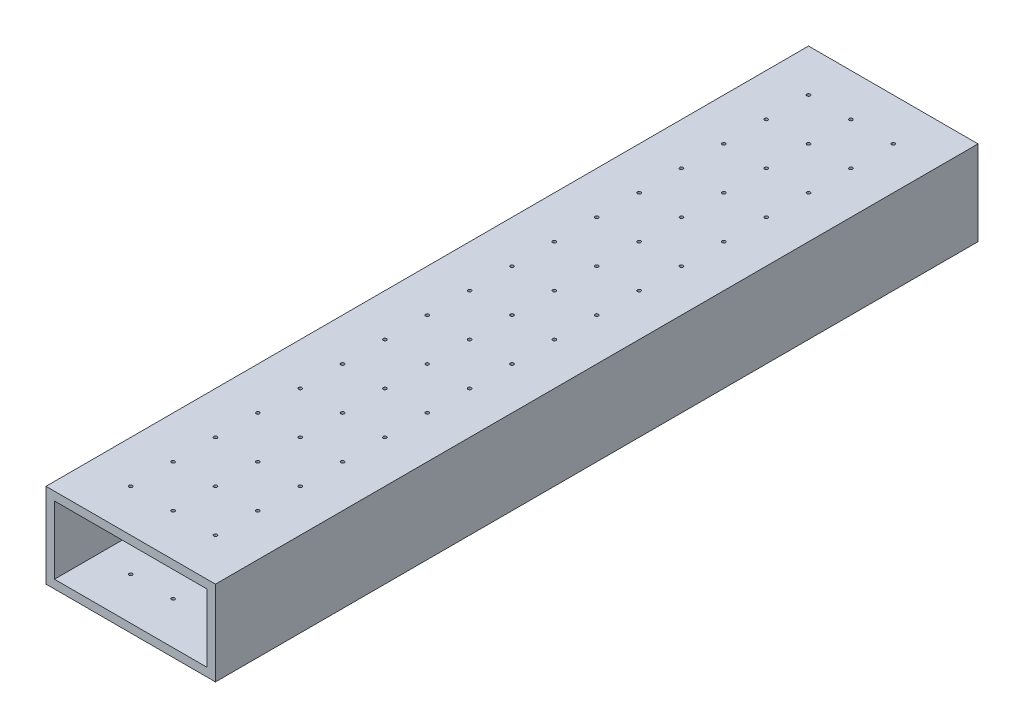
SolidWorks part; units mm, degrees
ref_plane "Front Plane" through (0, 0, 0) normal (0, 0, 1) x (1, 0, 0)
ref_plane "Top Plane" through (0, 0, 0) normal (0, 1, 0) x (1, 0, 0)
ref_plane "Right Plane" through (0, 0, 0) normal (1, 0, 0) x (0, 0, -1)
sketch "Sketch1" plane through (0, 0, 0) normal (0, 0, 1) x (1, 0, 0)
  line L1 (-24.4416, 12.2803) -> (26.3584, 12.2803)
  line L2 (-24.4416, 12.2803) -> (-24.4416, -13.1197)
  line L3 (-24.4416, -13.1197) -> (26.3584, -13.1197)
  line L4 (26.3584, 12.2803) -> (26.3584, -13.1197)
  line L5 (-21.9016, 9.7403) -> (23.8184, 9.7403)
  line L6 (-21.9016, 9.7403) -> (-21.9016, -10.5797)
  line L7 (-21.9016, -10.5797) -> (23.8184, -10.5797)
  line L8 (23.8184, 9.7403) -> (23.8184, -10.5797)
  dimension "D1" = 50.8
  dimension "D2" = 25.4
  dimension "D3" = 2.54
  dimension "D4" = 2.54
  dimension "D5" = 2.54
  dimension "D6" = 2.54
extrude "Boss-Extrude1" add sketch "Sketch1" along normal blind 228.6
sketch "Sketch2" plane through (0, 12.2803, 0) normal (0, 1, 0) x (1, 0, 0)
  line L0 (-24.4416, -228.6) -> (-24.4416, 0) construction
  line L1 (26.3584, -228.6) -> (-24.4416, -228.6) construction
  circle A0 centre (-11.7416, -215.9) radius 0.5
  circle A1 centre (0.9584, -215.9) radius 0.5
  circle A2 centre (13.6584, -215.9) radius 0.5
  circle A3 centre (0.9584, -203.2) radius 0.5
  circle A4 centre (13.6584, -203.2) radius 0.5
  circle A5 centre (0.9584, -190.5) radius 0.5
  circle A6 centre (13.6584, -190.5) radius 0.5
  circle A7 centre (0.9584, -177.8) radius 0.5
  circle A8 centre (13.6584, -177.8) radius 0.5
  circle A9 centre (0.9584, -165.1) radius 0.5
  circle A10 centre (13.6584, -165.1) radius 0.5
  circle A11 centre (0.9584, -152.4) radius 0.5
  circle A12 centre (13.6584, -152.4) radius 0.5
  circle A13 centre (0.9584, -139.7) radius 0.5
  circle A14 centre (13.6584, -139.7) radius 0.5
  circle A15 centre (0.9584, -127) radius 0.5
  circle A16 centre (13.6584, -127) radius 0.5
  circle A17 centre (0.9584, -114.3) radius 0.5
  circle A18 centre (13.6584, -114.3) radius 0.5
  circle A19 centre (0.9584, -101.6) radius 0.5
  circle A20 centre (13.6584, -101.6) radius 0.5
  circle A21 centre (0.9584, -88.9) radius 0.5
  circle A22 centre (13.6584, -88.9) radius 0.5
  circle A23 centre (0.9584, -76.2) radius 0.5
  circle A24 centre (13.6584, -76.2) radius 0.5
  circle A25 centre (0.9584, -63.5) radius 0.5
  circle A26 centre (13.6584, -63.5) radius 0.5
  circle A27 centre (0.9584, -50.8) radius 0.5
  circle A28 centre (13.6584, -50.8) radius 0.5
  circle A29 centre (0.9584, -38.1) radius 0.5
  circle A30 centre (13.6584, -38.1) radius 0.5
  circle A31 centre (0.9584, -25.4) radius 0.5
  circle A32 centre (13.6584, -25.4) radius 0.5
  circle A33 centre (0.9584, -12.7) radius 0.5
  circle A34 centre (13.6584, -12.7) radius 0.5
  circle A35 centre (-11.7416, -203.2) radius 0.5
  circle A36 centre (-11.7416, -190.5) radius 0.5
  circle A37 centre (-11.7416, -177.8) radius 0.5
  circle A38 centre (-11.7416, -165.1) radius 0.5
  circle A39 centre (-11.7416, -152.4) radius 0.5
  circle A40 centre (-11.7416, -139.7) radius 0.5
  circle A41 centre (-11.7416, -127) radius 0.5
  circle A42 centre (-11.7416, -114.3) radius 0.5
  circle A43 centre (-11.7416, -101.6) radius 0.5
  circle A44 centre (-11.7416, -88.9) radius 0.5
  circle A45 centre (-11.7416, -76.2) radius 0.5
  circle A46 centre (-11.7416, -63.5) radius 0.5
  circle A47 centre (-11.7416, -50.8) radius 0.5
  circle A48 centre (-11.7416, -38.1) radius 0.5
  circle A49 centre (-11.7416, -25.4) radius 0.5
  circle A50 centre (-11.7416, -12.7) radius 0.5
  dimension "D3" = 1
  dimension "D1" = 12.7
  dimension "D2" = 12.7
  dimension "D4" = 3
  dimension "D5" = 17
extrude "Cut-Extrude1" cut sketch "Sketch2" against normal through all both and the other way through all
